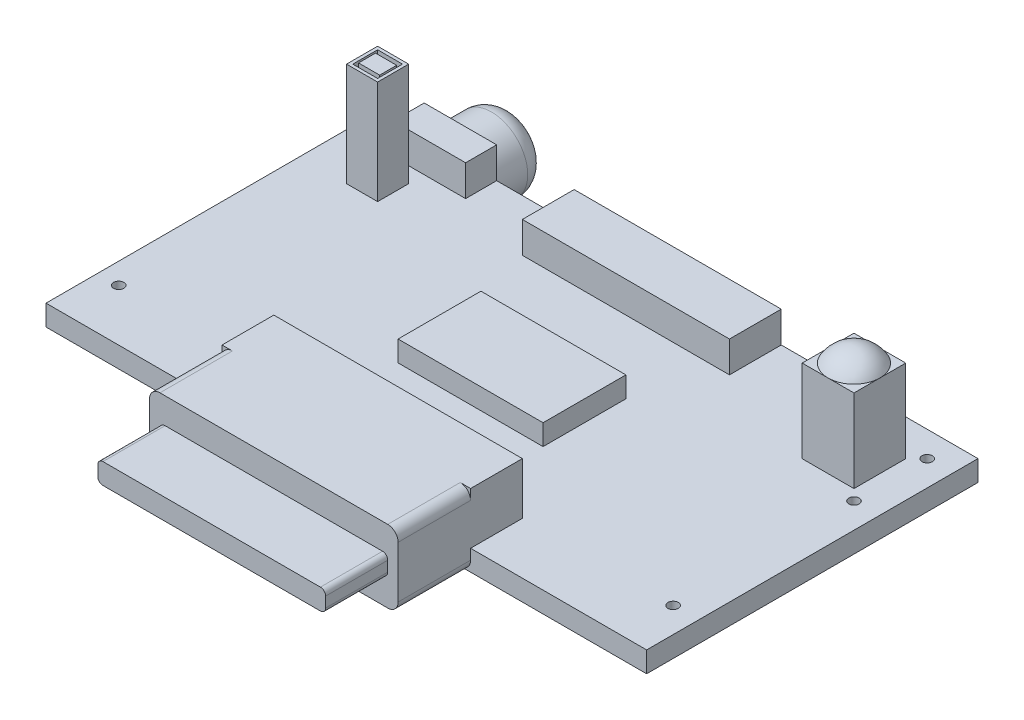
SolidWorks part; units mm, degrees
ref_plane "Front" through (0, 0, 0) normal (0, 0, 1) x (1, 0, 0)
ref_plane "Top" through (0, 0, 0) normal (0, 1, 0) x (1, 0, 0)
ref_plane "Right" through (0, 0, 0) normal (1, 0, 0) x (0, 0, -1)
sketch "Sketch1" plane through (0, 0, 0) normal (0, 1, 0) x (1, 0, 0)
  line L1 (0, 0) -> (58, 0)
  line L2 (0, 0) -> (0, -32)
  line L3 (0, -32) -> (58, -32)
  line L4 (58, 0) -> (58, -32)
  dimension "D1" = 32
  dimension "D2" = 58
extrude "Extrude1" add sketch "Sketch1" along normal blind 2
sketch "Sketch2" plane through (0, 2, 0) normal (0, 1, 0) x (-1, 0, 0)
  line L0 (-58, 32) -> (-58, 0) construction
  line L1 (-58, 0) -> (0, 0) construction
  line L2 (0, 0) -> (0, 32) construction
  line L3 (0, 32) -> (-58, 32) construction
  circle A0 centre (-55.557, 2.464) radius 0.5
  circle A1 centre (-55.557, 9.535) radius 0.5
  circle A2 centre (-55.557, 27) radius 0.5
  circle A3 centre (-2.022, 27) radius 0.5
  circle A4 centre (-2.022, 2.464) radius 0.5
  dimension "D5" = 1
  dimension "D1" = 2.443
  dimension "D2" = 2.464
  dimension "D3" = 2.022
  dimension "D4" = 5
  dimension "D6" = 7.071
extrude "Cut-Extrude1" cut sketch "Sketch2" against normal up to next
sketch "Sketch3" plane through (0, 2, 0) normal (0, 1, 0) x (-1, 0, 0)
  line L0 (-52.0214, 5.9995) -> (-54.5214, 8.4995) construction
  line L1 (-54.5214, 8.4995) -> (-49.5214, 8.4995)
  line L2 (-54.5214, 8.4995) -> (-54.5214, 3.4995)
  line L3 (-54.5214, 3.4995) -> (-49.5214, 3.4995)
  line L4 (-49.5214, 8.4995) -> (-49.5214, 3.4995)
  line L5 (-52.0214, 5.9995) -> (-49.5214, 8.4995) construction
  line L6 (-52.0214, 5.9995) -> (-49.5214, 3.4995) construction
  arc A0 (-55.557, 9.535) -> (-55.557, 2.464) centre (-52.0214, 5.9995) cw construction
  circle A1 centre (-55.557, 2.464) radius 0.5 construction
  circle A2 centre (-55.557, 9.535) radius 0.5 construction
  dimension "D1" = 5
  dimension "D2" = 5
extrude "Extrude2" add sketch "Sketch3" along normal blind 8
sketch "Sketch5" plane through (0, 10, 0) normal (0, 1, 0) x (-1, 0, 0)
  line L0 (-52.0214, 8.4995) -> (-52.0214, 3.4995) construction
  line L1 (-49.5214, 8.4995) -> (-54.5214, 8.4995) construction
  line L2 (-54.5214, 3.4995) -> (-49.5214, 3.4995) construction
ref_plane "Plane1" through (52.0214, 0, 0) normal (1, 0, 0) x (0, 0, -1)
sketch "Sketch6" plane through (52.0214, 0, 0) normal (1, 0, 0) x (0, 0, -1)
  line L0 (-10.0846, 11.4434) -> (-5.9995, 11.4434) construction
  line L1 (-3.4995, 10) -> (-5.9995, 10)
  line L2 (-8.4995, 10) -> (-3.4995, 10) construction
  line L3 (-5.9995, 11.4434) -> (-5.9995, 10)
  line L4 (-5.9995, 11.4434) -> (-5.9995, 10) construction
  arc A0 (-3.4995, 10) -> (-5.9995, 11.4434) centre (-5.9995, 8.5566) ccw
  dimension "D1" = 60
revolve "Revolve1" add sketch "Sketch6" angle 360 about L3
sketch "Sketch10" plane through (0, 2, 0) normal (0, 1, 0) x (-1, 0, 0)
  line L0 (-6.022, 7.5) -> (-6.022, 4.5) construction
  line L1 (-6.022, 2.464) -> (-2.022, 2.464) construction
  line L2 (-6.022, 2.464) -> (-6.022, 6) construction
  line L3 (-7.522, 4.5) -> (-4.522, 4.5)
  line L4 (-7.522, 4.5) -> (-7.522, 7.5)
  line L5 (-7.522, 7.5) -> (-4.522, 7.5)
  line L6 (-4.522, 4.5) -> (-4.522, 7.5)
  line L7 (-7.522, 6) -> (-4.522, 6) construction
  dimension "D1" = 4
  dimension "D2" = 3.536
  dimension "D3" = 3
  dimension "D4" = 3
extrude "flash led box" add sketch "Sketch10" along normal blind 9
sketch "Sketch12" plane through (0, 11, 0) normal (0, 1, 0) x (-1, 0, 0)
  line L4 (-7.522, 7.5) -> (-7.522, 4.5)
  line L5 (-7.522, 4.5) -> (-4.522, 4.5)
  line L6 (-4.522, 4.5) -> (-4.522, 7.5)
  line L7 (-4.522, 7.5) -> (-7.522, 7.5)
  line L8 (-7.522, 7.5) -> (-7.522, 4.5)
  line L9 (-7.522, 4.5) -> (-4.522, 4.5)
  line L10 (-4.522, 4.5) -> (-4.522, 7.5)
  line L11 (-4.522, 7.5) -> (-7.522, 7.5)
  line L16 (-7.222, 7.2) -> (-7.222, 4.8)
  line L17 (-7.222, 4.8) -> (-4.822, 4.8)
  line L18 (-4.822, 4.8) -> (-4.822, 7.2)
  line L19 (-4.822, 7.2) -> (-7.222, 7.2)
  line L20 (-7.222, 7.2) -> (-7.222, 4.8)
  line L21 (-7.222, 4.8) -> (-4.822, 4.8)
  line L22 (-4.822, 4.8) -> (-4.822, 7.2)
  line L23 (-4.822, 7.2) -> (-7.222, 7.2)
  dimension "D1" = 0
  dimension "D2" = 0.3
extrude "Extrude4" add sketch "Sketch12" along normal blind 1
sketch "Sketch13" plane through (0, 11, 0) normal (0, 1, 0) x (-1, 0, 0)
  line L0 (-6.022, 6.82) -> (-6.022, 7.2) construction
  line L1 (-7.042, 6.82) -> (-5.002, 6.82)
  line L2 (-7.042, 6.82) -> (-7.042, 5.18)
  line L3 (-7.042, 5.18) -> (-5.002, 5.18)
  line L4 (-5.002, 6.82) -> (-5.002, 5.18)
  line L5 (-4.822, 7.2) -> (-7.222, 7.2) construction
  line L6 (-6.022, 5.18) -> (-6.022, 4.8) construction
  line L7 (-7.222, 4.8) -> (-4.822, 4.8) construction
  dimension "D1" = 2.04
  dimension "D2" = 1.64
extrude "Extrude5" add sketch "Sketch13" along normal blind 1
sketch "Sketch14" plane through (0, 2, 0) normal (0, 1, 0) x (-1, 0, 0)
  line L0 (0, 32) -> (-58, 32) construction
  line L1 (-41, 32) -> (-17, 32)
  line L2 (-41, 32) -> (-41, 27)
  line L3 (-41, 27) -> (-17, 27)
  line L4 (-17, 32) -> (-17, 27)
  line L5 (0, 32) -> (-17, 32) construction
  line L6 (-41, 32) -> (-58, 32) construction
  dimension "D1" = 24
  dimension "D2" = 5
extrude "Extrude6" add sketch "Sketch14" along normal blind 5
sketch "Sketch16" plane through (0, 0, 32) normal (0, 0, 1) x (1, 0, 0)
  line L0 (0, 0) -> (58, 0) construction
  line L1 (18, 7) -> (40, 7)
  line L2 (17, 6) -> (17, 1)
  line L3 (18, 0) -> (40, 0)
  line L4 (41, 6) -> (41, 1)
  line L5 (41, 7) -> (41, 2) construction
  arc A0 (40, 7) -> (41, 6) centre (40, 6) cw
  arc A1 (40, 0) -> (41, 1) centre (40, 1) ccw
  arc A2 (17, 1) -> (18, 0) centre (18, 1) ccw
  arc A3 (18, 7) -> (17, 6) centre (18, 6) ccw
  point P13 (41, 0)
  point P18 (17, 7)
  dimension "D1" = 1
extrude "Extrude7" add sketch "Sketch16" along normal blind 7
sketch "Sketch17" plane through (0, 0, 39) normal (0, 0, 1) x (1, 0, 0)
  line L0 (29, 2.5) -> (29, 0) construction
  line L1 (18.5, 4.5) -> (39.5, 4.5)
  line L2 (18, 4) -> (18, 3)
  line L3 (18.5, 2.5) -> (39.5, 2.5)
  line L4 (40, 4) -> (40, 3)
  line L5 (18, 0) -> (40, 0) construction
  line L8 (41, 2) -> (17, 2) construction
  line L10 (29, 4.5) -> (29, 7) construction
  line L11 (40, 7) -> (18, 7) construction
  arc A0 (39.5, 2.5) -> (40, 3) centre (39.5, 3) ccw
  arc A1 (39.5, 4.5) -> (40, 4) centre (39.5, 4) cw
  arc A2 (18.5, 4.5) -> (18, 4) centre (18.5, 4) ccw
  arc A3 (18, 3) -> (18.5, 2.5) centre (18.5, 3) ccw
  dimension "D1" = 0.5
  dimension "D2" = 22
  dimension "D3" = 2
extrude "Extrude8" add sketch "Sketch17" along normal blind 6
sketch "Sketch18" plane through (0, 2, 0) normal (0, 1, 0) x (-1, 0, 0)
  line L0 (-58, 0) -> (0, 0) construction
  line L1 (-19, 0) -> (-39, 0)
  line L2 (-19, 0) -> (-19, 5)
  line L3 (-19, 5) -> (-39, 5)
  line L4 (-39, 0) -> (-39, 5)
  line L5 (-19, 0) -> (0, 0) construction
  line L6 (-39, 0) -> (-58, 0) construction
  dimension "D1" = 20
  dimension "D2" = 5
extrude "to lcd" add sketch "Sketch18" along normal blind 3
sketch "Sketch19" plane through (0, 2, 0) normal (0, 1, 0) x (-1, 0, 0)
  line L0 (-22, 16) -> (0, 16) construction
  line L1 (-36, 12) -> (-22, 12)
  line L2 (-36, 12) -> (-36, 20)
  line L3 (-36, 20) -> (-22, 20)
  line L4 (-22, 12) -> (-22, 20)
  line L5 (0, 0) -> (0, 32) construction
  line L6 (-36, 16) -> (-58, 16) construction
  line L7 (-58, 32) -> (-58, 0) construction
  dimension "D1" = 14
  dimension "D2" = 8
extrude "flash memory" add sketch "Sketch19" along normal blind 2
sketch "Sketch20" plane through (0, 2, 0) normal (0, 1, 0) x (-1, 0, 0)
  line L0 (3.98, 21.1298) -> (3.98, -10.0739) construction
  line L1 (0, 0) -> (0, 32) construction
  line L2 (-19, 0) -> (0, 0) construction
  line L3 (-11.52, 3) -> (-4.52, 3)
  line L4 (-11.52, 3) -> (-11.52, 0)
  line L5 (-11.52, 0) -> (-4.52, 0)
  line L6 (-4.52, 3) -> (-4.52, 0)
  line L7 (-8.02, 0) -> (-8.02, 3) construction
  dimension "D1" = 3.98
  dimension "D2" = 12
  dimension "D3" = 7
  dimension "D4" = 3
extrude "Extrude11" add sketch "Sketch20" along normal blind 3
sketch "Sketch21" plane through (0, 0, 0) normal (0, 0, -1) x (-1, 0, 0)
  line L0 (-4.52, 2) -> (-4.52, 1) construction
  line L1 (-4.52, 1) -> (-8.02, 1) construction
  line L2 (-8.02, 1) -> (-11.52, 1) construction
  line L3 (-11.52, 5) -> (-11.52, 2) construction
  circle A0 centre (-8.02, 1) radius 3.5
  dimension "D1" = 7
  dimension "D2" = 1
extrude "Extrude12" add sketch "Sketch21" along normal blind 5
fillet "Fillet1" radius 2 1 edges at (4.52, 1, -5)
